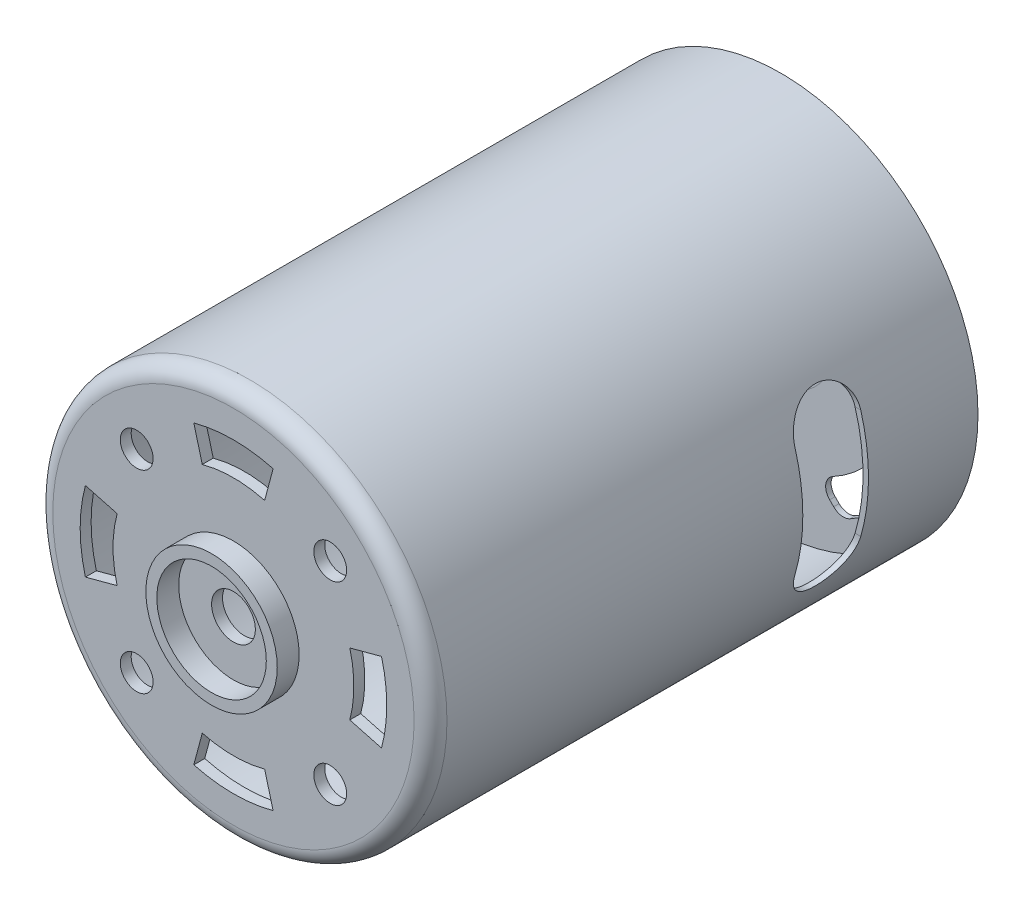
SolidWorks part; units mm, degrees
ref_plane "Alzado" through (0, 0, 0) normal (0, 0, 1) x (1, 0, 0)
ref_plane "Planta" through (0, 0, 0) normal (0, 1, 0) x (1, 0, 0)
ref_plane "Vista lateral" through (0, 0, 0) normal (1, 0, 0) x (0, 0, -1)
sketch "Croquis1" plane through (0, 0, 0) normal (0, 0, 1) x (1, 0, 0)
  circle A0 centre (0, 0) radius 18
  circle A1 centre (0, 0) radius 17.5
  dimension "D1" = 36
  dimension "D2" = 35
extrude "Saliente-Extruir1" add sketch "Croquis1" along normal blind 50
sketch "Croquis2" plane through (0, 0, 50) normal (0, 0, 1) x (1, 0, 0)
  circle A0 centre (0, 0) radius 17.5
  circle A1 centre (0, 0) radius 17.5 construction
extrude "Saliente-Extruir2" add sketch "Croquis2" against normal blind 1
sketch "Croquis5" plane through (0, 0, 0) normal (1, 0, 0) x (0, 0, -1)
  line L0 (0, 0) -> (-10, 0) construction
  line L1 (-10, 0) -> (-13, 0) construction
  line L2 (-13, 5) -> (-13, -5) construction
  line L3 (-10, 5) -> (-10, -5)
  line L4 (-16, 5) -> (-16, -5)
  arc A0 (-10, 5) -> (-16, 5) centre (-13, 5) ccw
  arc A1 (-16, -5) -> (-10, -5) centre (-13, -5) ccw
  point P6 (-13, 0)
  dimension "D4" = 10
  dimension "D1" = 10
  dimension "D2" = 3
  dimension "D3" = 6
extrude "Cortar-Extruir1" cut sketch "Croquis5" against normal mid plane 38
fillet "Redondeo1" radius 1.5 2 edges at (18, 0, 50) (17.5, 0, 49)
sketch "Sketch1" plane through (0, 0, 50) normal (0, 0, 1) x (1, 0, 0)
  circle A0 centre (0, 0) radius 2
  dimension "D1" = 4
extrude "Cut-Extrude1" cut sketch "Sketch1" against normal blind 10
sketch "Sketch2" plane through (0, 0, 0) normal (1, 0, 0) x (0, 0, -1)
  line L0 (0, 0) -> (-5.0182, 0) construction
  line L3 (0, -2) -> (-0.5, -2) construction
  line L4 (-0.5, -2) -> (-0.5, -3.9301)
  line L5 (0, -2) -> (0, 0) construction
  line L7 (-1, -17.5) -> (-1, -5.914)
  line L8 (-0.8356, -5.12) -> (-0.6644, -4.7241)
  line L9 (0, -2) -> (0, -4.0336)
  line L10 (-0.3356, -5.2235) -> (-0.1644, -4.8277)
  line L12 (-1, -17.5) -> (-0.5, -17.5)
  line L13 (-0.5, -16.987) -> (-0.5, -5.6035) construction
  line L14 (-0.5, -2) -> (0, -2)
  line L15 (-0.5, -5.6035) -> (0, -4.4476) construction
  line L16 (0, -2) -> (0, -4.4476) construction
  line L17 (-1, -17.5) -> (-1, -5.5) construction
  line L18 (-1, -5.5) -> (-0.5, -4.3441) construction
  line L19 (-0.5, -2) -> (-0.5, -4.3441) construction
  line L20 (-0.2101, -16.9796) -> (-0.5, -16.987) construction
  line L21 (-0.1973, -17.4795) -> (-1, -17.5) construction
  line L22 (-0.5, -17.5) -> (-0.5, -6.0176)
  line L23 (-0.5, -17.5) -> (-0.5, -18) construction
  line L24 (-48.5, -18) -> (0, -18) construction
  line L25 (0, -18) -> (0, 18) construction
  arc A0 (-0.3356, -5.2235) -> (-0.5, -6.0176) centre (1.5, -6.0175) ccw
  arc A1 (0, -4.0336) -> (-0.1644, -4.8277) centre (-2, -4.0336) cw
  arc A2 (-1, -5.914) -> (-0.8356, -5.12) centre (1, -5.914) cw
  arc A3 (-0.5, -3.9301) -> (-0.6644, -4.7241) centre (-2.5, -3.9301) cw
  point P28 (-1, -5.5)
  dimension "D6" = 2
  dimension "D1" = 0.5
  dimension "D2" = 12
  dimension "D3" = 2
  dimension "D4" = 0.5
  dimension "D7" = 0.5
  dimension "D5" = 0.5
revolve "Revolve1" add sketch "Sketch2" angle 360 about L0
sketch "Sketch3" plane through (0, 0, 0.5) normal (0, 0, -1) x (-1, 0, 0)
  line L0 (-12.5216, 5.4506) -> (-12.8897, 5.8186)
  line L1 (-5.4506, 12.5216) -> (-5.8186, 12.8897)
  line L4 (-5.4506, -12.5216) -> (-5.8186, -12.8897)
  line L5 (5.4506, 12.5216) -> (5.8186, 12.8897)
  line L12 (-12.5216, -5.4506) -> (-12.8897, -5.8186)
  line L13 (12.5216, 5.4506) -> (12.8897, 5.8186)
  line L14 (12.5216, -5.4506) -> (12.8897, -5.8186)
  line L15 (5.4506, -12.5216) -> (5.8186, -12.8897)
  arc A2 (-10.5398, -5.7369) -> (-5.7369, -10.5398) centre (0, 0) ccw
  arc A25 (-13.0972, -7.3118) -> (-7.3118, -13.0972) centre (0, 0) ccw
  arc A27 (-12.5216, -5.4506) -> (-10.5398, -5.7369) centre (-11.6378, -6.3344) cw
  arc A28 (-12.8897, -5.8186) -> (-13.0972, -7.3118) centre (-12.0058, -6.7025) ccw
  arc A29 (-5.4506, -12.5216) -> (-5.7369, -10.5398) centre (-6.3344, -11.6378) ccw
  arc A30 (-5.8186, -12.8897) -> (-7.3118, -13.0972) centre (-6.7025, -12.0058) cw
  arc A31 (-5.7369, 10.5398) -> (-10.5398, 5.7369) centre (0, 0) ccw
  arc A32 (-12.5216, 5.4506) -> (-10.5398, 5.7369) centre (-11.6378, 6.3344) ccw
  arc A33 (-5.4506, 12.5216) -> (-5.7369, 10.5398) centre (-6.3344, 11.6378) cw
  arc A34 (-12.8897, 5.8186) -> (-13.0972, 7.3118) centre (-12.0058, 6.7025) cw
  arc A35 (-7.3118, 13.0972) -> (-13.0972, 7.3118) centre (0, 0) ccw
  arc A36 (-5.8186, 12.8897) -> (-7.3118, 13.0972) centre (-6.7025, 12.0058) ccw
  arc A37 (10.5398, 5.7369) -> (5.7369, 10.5398) centre (0, 0) ccw
  arc A38 (5.4506, 12.5216) -> (5.7369, 10.5398) centre (6.3344, 11.6378) ccw
  arc A39 (12.5216, 5.4506) -> (10.5398, 5.7369) centre (11.6378, 6.3344) cw
  arc A40 (5.8186, 12.8897) -> (7.3118, 13.0972) centre (6.7025, 12.0058) cw
  arc A41 (13.0972, 7.3118) -> (7.3118, 13.0972) centre (0, 0) ccw
  arc A42 (12.8897, 5.8186) -> (13.0972, 7.3118) centre (12.0058, 6.7025) ccw
  arc A43 (5.7369, -10.5398) -> (10.5398, -5.7369) centre (0, 0) ccw
  arc A44 (12.5216, -5.4506) -> (10.5398, -5.7369) centre (11.6378, -6.3344) ccw
  arc A45 (5.4506, -12.5216) -> (5.7369, -10.5398) centre (6.3344, -11.6378) cw
  arc A46 (12.8897, -5.8186) -> (13.0972, -7.3118) centre (12.0058, -6.7025) cw
  arc A47 (7.3118, -13.0972) -> (13.0972, -7.3118) centre (0, 0) ccw
  arc A48 (5.8186, -12.8897) -> (7.3118, -13.0972) centre (6.7025, -12.0058) ccw
  point P54 (0, 0)
  dimension "D1" = 1.25
extrude "Cut-Extrude2" cut sketch "Sketch3" against normal blind 10
sketch "Sketch4" plane through (0, 0, 0) normal (0, 0, -1) x (-1, 0, 0)
  line L0 (0, -17.5) -> (0, -17.75) construction
  line L1 (0, 0) -> (1.5, 0) construction
  line L2 (0, 0) -> (-1.5, 0) construction
  line L3 (1.5, -17.4356) -> (1.5, -17.6865)
  line L4 (-1.5, -17.4356) -> (-1.5, -17.6865)
  line L5 (-14.3497, -10.0168) -> (-14.567, -10.1423)
  line L6 (-15.8497, -7.4188) -> (-16.067, -7.5442)
  line L7 (-15.8497, 7.4188) -> (-16.067, 7.5442)
  line L8 (-14.3497, 10.0168) -> (-14.567, 10.1423)
  line L9 (-1.5, 17.4356) -> (-1.5, 17.6865)
  line L10 (1.5, 17.4356) -> (1.5, 17.6865)
  line L11 (14.3497, 10.0168) -> (14.567, 10.1423)
  line L12 (15.8497, 7.4188) -> (16.067, 7.5442)
  line L13 (15.8497, -7.4188) -> (16.067, -7.5442)
  line L14 (14.3497, -10.0168) -> (14.567, -10.1423)
  arc A1 (-1.5, -17.4356) -> (1.5, -17.4356) centre (0, 0) ccw
  arc A3 (-1.5, -17.6865) -> (1.5, -17.6865) centre (0, 0) ccw
  arc A4 (-16.067, -7.5442) -> (-14.567, -10.1423) centre (0, 0) ccw
  arc A5 (-15.8497, -7.4188) -> (-14.3497, -10.0168) centre (0, 0) ccw
  arc A6 (-14.567, 10.1423) -> (-16.067, 7.5442) centre (0, 0) ccw
  arc A7 (-14.3497, 10.0168) -> (-15.8497, 7.4188) centre (0, 0) ccw
  arc A8 (1.5, 17.6865) -> (-1.5, 17.6865) centre (0, 0) ccw
  arc A9 (1.5, 17.4356) -> (-1.5, 17.4356) centre (0, 0) ccw
  arc A10 (16.067, 7.5442) -> (14.567, 10.1423) centre (0, 0) ccw
  arc A11 (15.8497, 7.4188) -> (14.3497, 10.0168) centre (0, 0) ccw
  arc A12 (14.567, -10.1423) -> (16.067, -7.5442) centre (0, 0) ccw
  arc A13 (14.3497, -10.0168) -> (15.8497, -7.4188) centre (0, 0) ccw
  point P34 (0, 0)
  dimension "D1" = 1.5
  dimension "D2" = 1.5
extrude "Cut-Extrude3" cut sketch "Sketch4" against normal blind 0.5
sketch "Sketch5" plane through (0, 0, 0.5) normal (0, 0, -1) x (-1, 0, 0)
  line L0 (1.5, -17.6865) -> (1.5, -17.4356)
  line L1 (-1.5, -17.6865) -> (-1.5, -17.4356)
  line L2 (-14.567, -10.1423) -> (-14.3497, -10.0168)
  line L3 (-16.067, -7.5442) -> (-15.8497, -7.4188)
  line L4 (-16.067, 7.5442) -> (-15.8497, 7.4188)
  line L5 (-14.567, 10.1423) -> (-14.3497, 10.0168)
  line L6 (-1.5, 17.6865) -> (-1.5, 17.4356)
  line L7 (1.5, 17.6865) -> (1.5, 17.4356)
  line L8 (14.567, 10.1423) -> (14.3497, 10.0168)
  line L9 (16.067, 7.5442) -> (15.8497, 7.4188)
  line L10 (16.067, -7.5442) -> (15.8497, -7.4188)
  line L11 (14.567, -10.1423) -> (14.3497, -10.0168)
  arc A0 (-1.5, -17.6865) -> (1.5, -17.6865) centre (0, 0) ccw
  arc A2 (-1.5, -17.4356) -> (1.5, -17.4356) centre (0, 0) ccw
  arc A3 (-15.8497, -7.4188) -> (-14.3497, -10.0168) centre (0, 0) ccw
  arc A4 (-16.067, -7.5442) -> (-14.567, -10.1423) centre (0, 0) ccw
  arc A5 (-14.3497, 10.0168) -> (-15.8497, 7.4188) centre (0, 0) ccw
  arc A6 (-14.567, 10.1423) -> (-16.067, 7.5442) centre (0, 0) ccw
  arc A7 (1.5, 17.4356) -> (-1.5, 17.4356) centre (0, 0) ccw
  arc A8 (1.5, 17.6865) -> (-1.5, 17.6865) centre (0, 0) ccw
  arc A9 (15.8497, 7.4188) -> (14.3497, 10.0168) centre (0, 0) ccw
  arc A10 (16.067, 7.5442) -> (14.567, 10.1423) centre (0, 0) ccw
  arc A11 (14.3497, -10.0168) -> (15.8497, -7.4188) centre (0, 0) ccw
  arc A12 (14.567, -10.1423) -> (16.067, -7.5442) centre (0, 0) ccw
  point P33 (0, 0)
extrude "Boss-Extrude1" add sketch "Sketch5" along normal blind 0.5 separate body
sketch "Sketch7" plane through (0, 0, 0.5) normal (0, 0, -1) x (-1, 0, 0)
  line L0 (-1.5, -17.4356) -> (-1.5, -16.6856)
  line L2 (1.5, -16.6856) -> (1.5, -17.4356)
  line L3 (-15.8497, -7.4188) -> (-15.2001, -7.0438)
  line L4 (-13.7001, -9.6418) -> (-14.3497, -10.0168)
  line L5 (-14.3497, 10.0168) -> (-13.7001, 9.6418)
  line L6 (-15.2001, 7.0438) -> (-15.8497, 7.4188)
  line L7 (1.5, 17.4356) -> (1.5, 16.6856)
  line L8 (-1.5, 16.6856) -> (-1.5, 17.4356)
  line L9 (15.8497, 7.4188) -> (15.2001, 7.0438)
  line L10 (13.7001, 9.6418) -> (14.3497, 10.0168)
  line L11 (14.3497, -10.0168) -> (13.7001, -9.6418)
  line L12 (15.2001, -7.0438) -> (15.8497, -7.4188)
  arc A0 (-1.5, -17.4356) -> (1.5, -17.4356) centre (0, 0) ccw
  arc A1 (1.5, -16.6856) -> (-1.5, -16.6856) centre (0, -16.9184) ccw
  arc A2 (-13.7001, -9.6418) -> (-15.2001, -7.0438) centre (-14.6517, -8.4592) ccw
  arc A3 (-15.8497, -7.4188) -> (-14.3497, -10.0168) centre (0, 0) ccw
  arc A4 (-15.2001, 7.0438) -> (-13.7001, 9.6418) centre (-14.6517, 8.4592) ccw
  arc A5 (-14.3497, 10.0168) -> (-15.8497, 7.4188) centre (0, 0) ccw
  arc A6 (-1.5, 16.6856) -> (1.5, 16.6856) centre (0, 16.9184) ccw
  arc A7 (1.5, 17.4356) -> (-1.5, 17.4356) centre (0, 0) ccw
  arc A8 (13.7001, 9.6418) -> (15.2001, 7.0438) centre (14.6517, 8.4592) ccw
  arc A9 (15.8497, 7.4188) -> (14.3497, 10.0168) centre (0, 0) ccw
  arc A10 (15.2001, -7.0438) -> (13.7001, -9.6418) centre (14.6517, -8.4592) ccw
  arc A11 (14.3497, -10.0168) -> (15.8497, -7.4188) centre (0, 0) ccw
  point P37 (0, 0)
  dimension "D1" = 0.75
  dimension "D2" = 0.75
extrude "Boss-Extrude5" add sketch "Sketch7" along normal blind 0.1 separate body
sketch "Sketch8" plane through (0, 0, 0.5) normal (0, 0, -1) x (-1, 0, 0)
  line L0 (0, 0) -> (-12, 0) construction
  line L1 (0, 0) -> (0, 2.9555) construction
  line L2 (-12.75, 2) -> (-11.25, 2)
  line L3 (-12.75, 2) -> (-12.75, -2)
  line L4 (-12.75, -2) -> (-11.25, -2)
  line L5 (-11.25, 2) -> (-11.25, -2)
  line L6 (-12.75, 2) -> (-11.25, -2) construction
  line L7 (-12.75, -2) -> (-11.25, 2) construction
  line L8 (12.75, -2) -> (11.25, -2)
  line L9 (11.25, 2) -> (11.25, -2)
  line L10 (12.75, 2) -> (11.25, 2)
  line L11 (12.75, 2) -> (12.75, -2)
  dimension "D1" = 12
  dimension "D2" = 1.5
  dimension "D3" = 4
extrude "Cut-Extrude4" cut sketch "Sketch8" against normal blind 10
sketch "Sketch9" plane through (0, 0, 50) normal (0, 0, 1) x (1, 0, 0)
  line L0 (0, 0) -> (8.8388, 8.8388) construction
  line L1 (0, 0) -> (0, 11) construction
  line L2 (0, 0) -> (2.847, 10.6252) construction
  line L3 (0, 0) -> (-2.847, 10.6252) construction
  line L4 (-2.847, 10.6252) -> (-3.6235, 13.523)
  line L5 (2.847, 10.6252) -> (3.6235, 13.523)
  line L6 (10.6252, 2.847) -> (13.523, 3.6235)
  line L7 (10.6252, -2.847) -> (13.523, -3.6235)
  line L8 (2.847, -10.6252) -> (3.6235, -13.523)
  line L9 (-2.847, -10.6252) -> (-3.6235, -13.523)
  line L10 (-10.6252, -2.847) -> (-13.523, -3.6235)
  line L11 (-10.6252, 2.847) -> (-13.523, 3.6235)
  circle A0 centre (8.8388, 8.8388) radius 1.5
  arc A1 (3.6235, 13.523) -> (-3.6235, 13.523) centre (0, 0) ccw
  arc A2 (2.847, 10.6252) -> (-2.847, 10.6252) centre (0, 0) ccw
  arc A3 (13.523, -3.6235) -> (13.523, 3.6235) centre (0, 0) ccw
  arc A4 (10.6252, -2.847) -> (10.6252, 2.847) centre (0, 0) ccw
  circle A5 centre (8.8388, -8.8388) radius 1.5
  arc A6 (-3.6235, -13.523) -> (3.6235, -13.523) centre (0, 0) ccw
  arc A7 (-2.847, -10.6252) -> (2.847, -10.6252) centre (0, 0) ccw
  circle A8 centre (-8.8388, -8.8388) radius 1.5
  arc A9 (-13.523, 3.6235) -> (-13.523, -3.6235) centre (0, 0) ccw
  arc A10 (-10.6252, 2.847) -> (-10.6252, -2.847) centre (0, 0) ccw
  circle A11 centre (-8.8388, 8.8388) radius 1.5
  point P30 (0, 0)
  dimension "D1" = 28
  dimension "D2" = 22
  dimension "D3" = 3
  dimension "D4" = 45
  dimension "D5" = 12.5
  dimension "D6" = 15
  dimension "D7" = 15
  dimension "D8" = 4
extrude "Cut-Extrude5" cut sketch "Sketch9" against normal blind 10
sketch "Sketch10" plane through (0, 0, 50) normal (0, 0, 1) x (1, 0, 0)
  circle A0 centre (0, 0) radius 5
  circle A1 centre (0, 0) radius 6
  dimension "D1" = 10
  dimension "D2" = 12
extrude "Boss-Extrude6" add sketch "Sketch10" along normal blind 2
